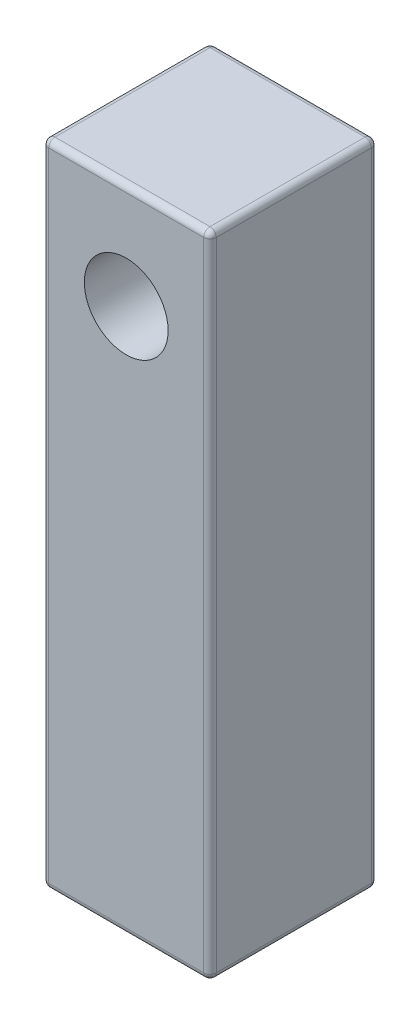
SolidWorks part; units mm, degrees
ref_plane "Ebene vorne" through (0, 0, 0) normal (0, 0, 1) x (1, 0, 0)
ref_plane "Ebene oben" through (0, 0, 0) normal (0, 1, 0) x (1, 0, 0)
ref_plane "Ebene rechts" through (0, 0, 0) normal (1, 0, 0) x (0, 0, -1)
sketch "Skizze1" plane through (0, 0, 0) normal (0, 1, 0) x (1, 0, 0)
  line L1 (-4, 4) -> (4, 4)
  line L2 (-4, 4) -> (-4, -4)
  line L3 (-4, -4) -> (4, -4)
  line L4 (4, 4) -> (4, -4)
  line L5 (-4, 4) -> (4, -4) construction
  line L6 (-4, -4) -> (4, 4) construction
  point P0 (0, 0)
  dimension "D1" = 8
extrude "Aufsatz-Linear austragen1" add sketch "Skizze1" along normal blind 31
fillet "Verrundung1" radius 0.3 12 edges at (4, 0, 0) (0, 0, -4) (-4, 0, 0) (0, 0, 4) (4, 31, 0) (0, 31, -4) (-4, 31, 0) (4, 15.5, 4) (-4, 15.5, 4) (-4, 15.5, -4) (4, 15.5, -4) (0, 31, 4)
sketch "Skizze2" plane through (0, 0, 4) normal (0, 0, 1) x (1, 0, 0)
  line L0 (-3.7, 31) -> (3.7, 31) construction
  line L1 (3.7, 30.7) -> (-3.7, 30.7) construction
  circle A0 centre (0, 26) radius 2
  point P4 (0, 0)
  point P7 (0, 30.7)
  dimension "D1" = 4
  dimension "D2" = 5
extrude "Schnitt-Linear austragen1" cut sketch "Skizze2" against normal through all
